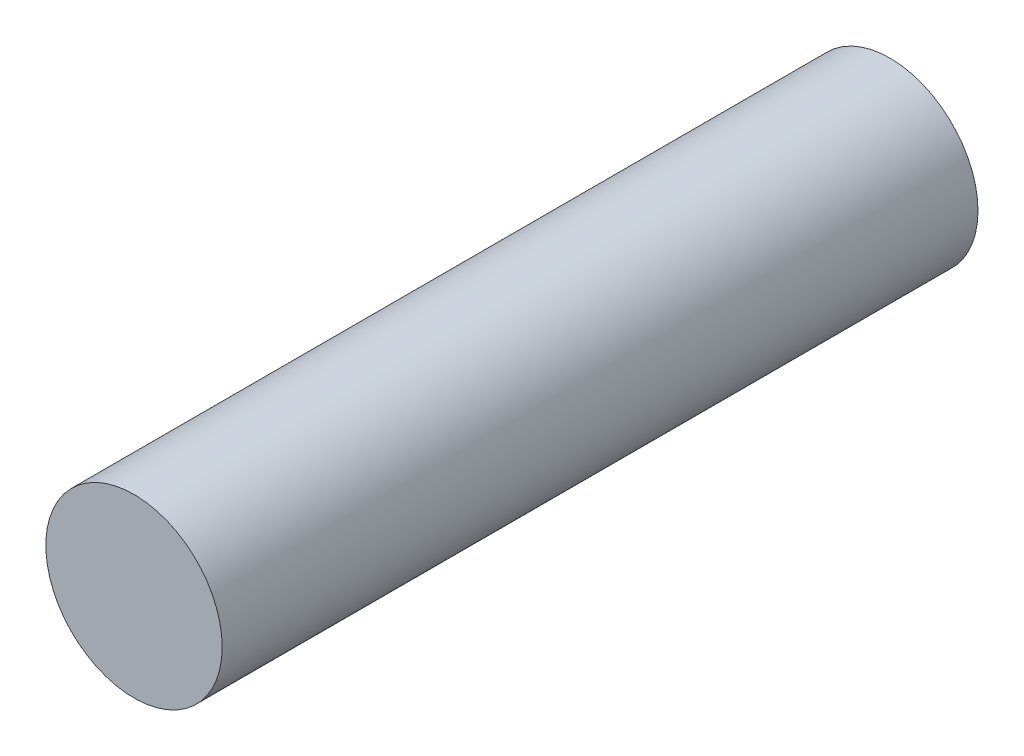
SolidWorks part; units mm, degrees
ref_plane "Ebene vorne" through (0, 0, 0) normal (0, 0, 1) x (1, 0, 0)
ref_plane "Ebene oben" through (0, 0, 0) normal (0, 1, 0) x (1, 0, 0)
ref_plane "Ebene rechts" through (0, 0, 0) normal (1, 0, 0) x (0, 0, -1)
sketch "Skizze1" plane through (0, 0, 0) normal (0, 0, 1) x (1, 0, 0)
  circle A0 centre (0, 0) radius 2.1
  dimension "D1" = 4.2
extrude "Aufsatz-Linear austragen1" add sketch "Skizze1" along normal blind 18
